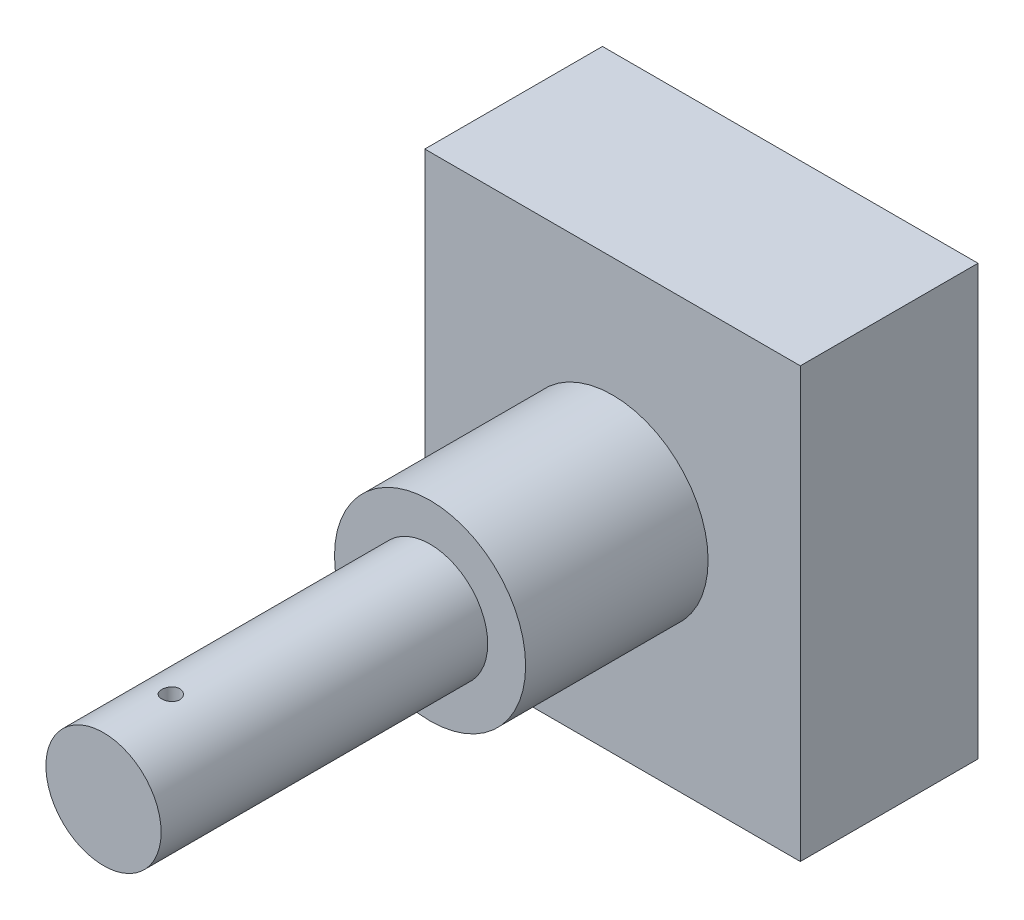
SolidWorks part; units mm, degrees
ref_plane "Front Plane" through (0, 0, 0) normal (0, 0, 1) x (1, 0, 0)
ref_plane "Top Plane" through (0, 0, 0) normal (0, 1, 0) x (1, 0, 0)
ref_plane "Right Plane" through (0, 0, 0) normal (1, 0, 0) x (0, 0, -1)
sketch "Sketch1" plane through (0, 0, 0) normal (0, 0, 1) x (1, 0, 0)
  circle A0 centre (0, 0) radius 4.975
  dimension "D1" = 9.95
extrude "Boss-Extrude1" add sketch "Sketch1" along normal blind 9.5
sketch "Sketch2" plane through (0, 0, 9.5) normal (0, 0, 1) x (1, 0, 0)
  circle A0 centre (0, 0) radius 3
  dimension "D1" = 6
extrude "Boss-Extrude2" add sketch "Sketch2" along normal blind 17
sketch "Sketch3" plane through (0, 0, 0) normal (0, 1, 0) x (1, 0, 0)
  line L0 (4.975, 0) -> (-4.975, 0) construction
  circle A0 centre (0, -23) radius 0.4659
  dimension "D1" = 23
extrude "Cut-Extrude1" cut sketch "Sketch3" against normal up to next and the other way up to next
sketch "Sketch5" plane through (0, 0, 0) normal (0, 0, -1) x (-1, 0, 0)
  line L1 (-9.775, 11.175) -> (9.775, 11.175)
  line L2 (-9.775, 11.175) -> (-9.775, -11.175)
  line L3 (-9.775, -11.175) -> (9.775, -11.175)
  line L4 (9.775, 11.175) -> (9.775, -11.175)
  line L5 (-9.775, 11.175) -> (9.775, -11.175) construction
  line L6 (-9.775, -11.175) -> (9.775, 11.175) construction
  point P0 (0, 0)
  dimension "D1" = 19.55
  dimension "D2" = 22.35
extrude "Boss-Extrude4" add sketch "Sketch5" along normal blind 9.25
